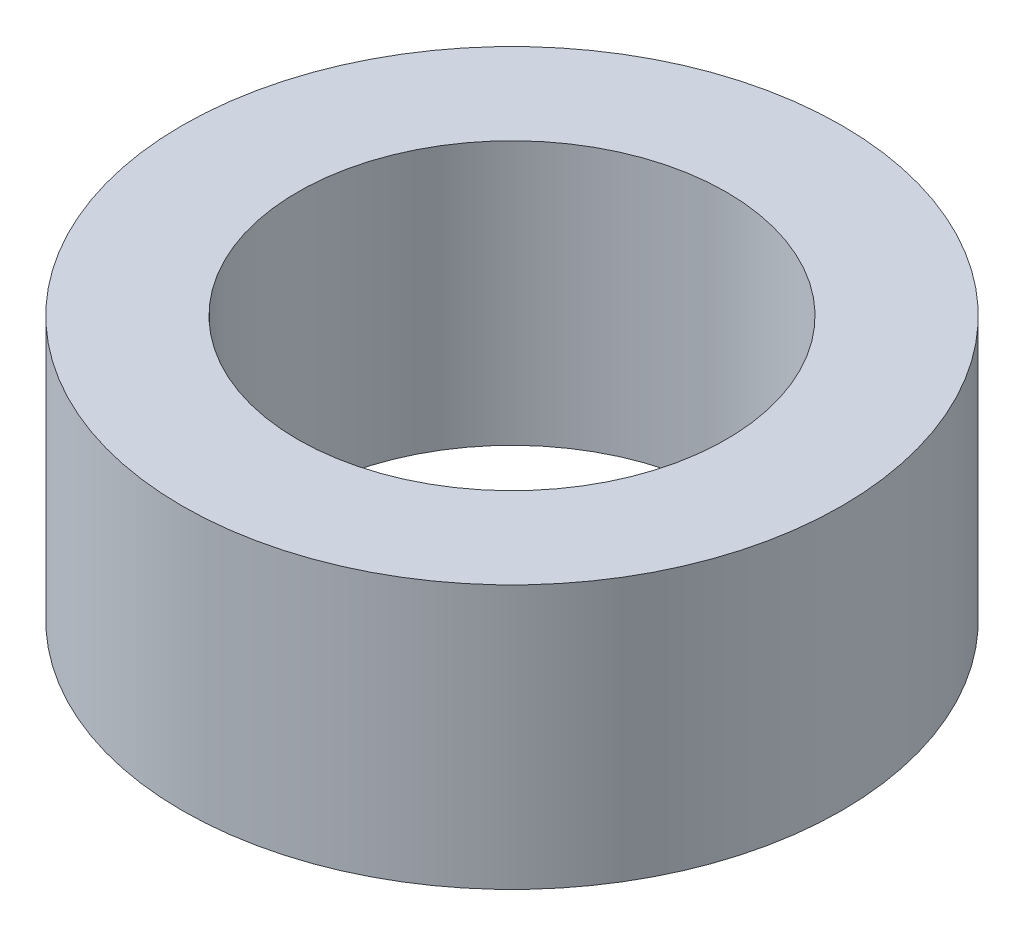
SolidWorks part; units mm, degrees
ref_plane "Front Plane" through (0, 0, 0) normal (0, 0, 1) x (1, 0, 0)
ref_plane "Top Plane" through (0, 0, 0) normal (0, 1, 0) x (1, 0, 0)
ref_plane "Right Plane" through (0, 0, 0) normal (1, 0, 0) x (0, 0, -1)
sketch "Sketch1" plane through (0, 0, 0) normal (0, 1, 0) x (1, 0, 0)
  circle A0 centre (0, 0) radius 4.875
  circle A1 centre (0, 0) radius 7.5
  dimension "D1" = 9.75
  dimension "D2" = 15
extrude "Boss-Extrude1" add sketch "Sketch1" along normal blind 6
